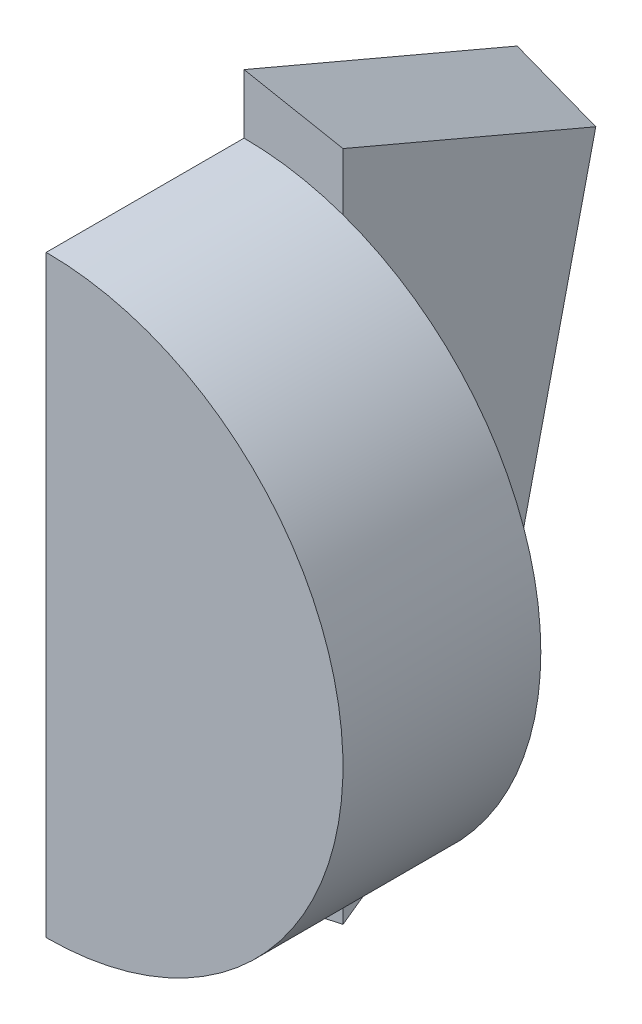
SolidWorks part; units mm, degrees
ref_plane "Front Plane" through (0, 0, 0) normal (0, 0, 1) x (1, 0, 0)
ref_plane "Top Plane" through (0, 0, 0) normal (0, 1, 0) x (1, 0, 0)
ref_plane "Right Plane" through (0, 0, 0) normal (1, 0, 0) x (0, 0, -1)
sketch "Sketch1" plane through (0, 0, 0) normal (0, 0, 1) x (1, 0, 0)
  line L0 (0, 150) -> (0, -150)
  arc A0 (0, -150) -> (0, 150) centre (0, 0) ccw
  point P6 (0, 0)
extrude "Boss-Extrude1" add sketch "Sketch1" along normal blind 100
sketch "Sketch2" plane through (0, 0, 0) normal (-1, 0, 0) x (0, 0, 1)
  line L0 (0, 180) -> (0, -180)
  line L1 (0, 180) -> (-138.0378, 121.3011)
  line L2 (-138.0378, 121.3011) -> (-81.6426, -122.255)
  line L3 (-81.6426, -122.255) -> (0, -180)
  line L4 (0, 150) -> (0, -150) construction
  dimension "D1" = 180
  dimension "D2" = 180
  dimension "D3" = 100
  dimension "D4" = 150
  dimension "D5" = 250
  dimension "D6" = 100
extrude "Boss-Extrude2" add sketch "Sketch2" against normal blind 50 contours L3 L0 L1 L2
draft "Draft1" type of draft neutral plane draft angle 10 neutral plane "Right Plane" faces to draft 3 face at (25, -151.1275, -40.8213) face at (25, 150.6505, -69.0189) face at (25, -0.477, -109.8402) neutral plane through (0, 0, 0) neutral plane normal (1, 0, 0) parameters "D1"=10
